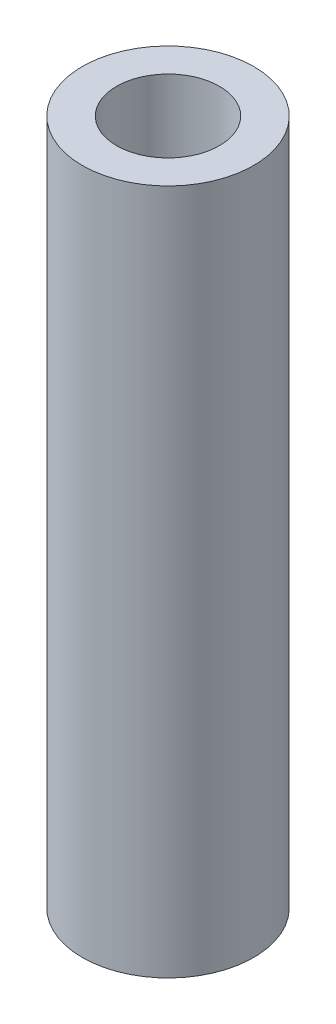
SolidWorks part; units mm, degrees
ref_plane "Front Plane" through (0, 0, 0) normal (0, 0, 1) x (1, 0, 0)
ref_plane "Top Plane" through (0, 0, 0) normal (0, 1, 0) x (1, 0, 0)
ref_plane "Right Plane" through (0, 0, 0) normal (1, 0, 0) x (0, 0, -1)
sketch "Sketch1" plane through (0, 0, 0) normal (0, 1, 0) x (1, 0, 0)
  circle A0 centre (0, 0) radius 2.5
  circle A1 centre (0, 0) radius 1.5
  dimension "D1" = 5
  dimension "D2" = 3
extrude "Boss-Extrude1" add sketch "Sketch1" along normal blind 20
